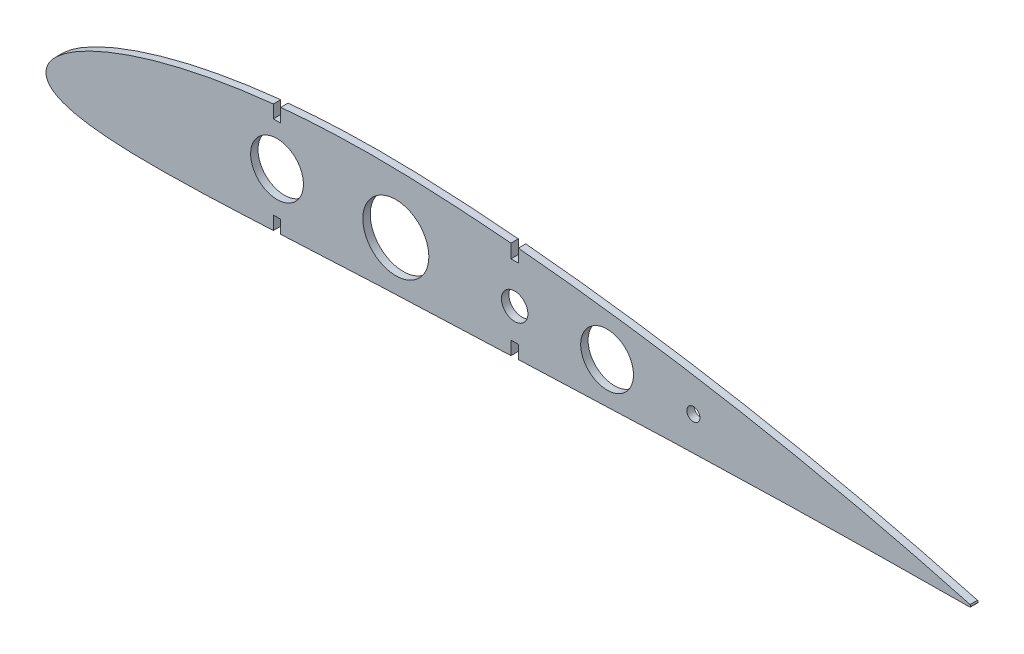
SolidWorks part; units mm, degrees
material "Сосна обыкновенная"
ref_plane "Front Plane" through (0, 0, 0) normal (0, 0, 1) x (1, 0, 0)
ref_plane "Top Plane" through (0, 0, 0) normal (0, 1, 0) x (1, 0, 0)
ref_plane "Right Plane" through (0, 0, 0) normal (1, 0, 0) x (0, 0, -1)
curve "Кривая1"
  spline degree 3 poles (0.0672, 0.87, 0) (0.0318, 0.5229, 0) (-0.0389, -0.1715, 0) (0.1092, -1.2382, 0) (0.4896, -2.2944, 0) (1.1401, -3.3111, 0) (2.0489, -4.255, 0) (3.2074, -5.1254, 0) (4.6283, -5.9301, 0) (6.3494, -6.6831, 0) (8.4416, -7.3951, 0) (11.0166, -8.0714, 0) (14.2364, -8.7104, 0) (18.3056, -9.2955, 0) (23.4194, -9.7901, 0) (29.6659, -10.1463, 0) (36.96, -10.3273, 0) (45.0764, -10.3268, 0) (53.7569, -10.166, 0) (62.8007, -9.8793, 0) (72.0812, -9.501, 0) (81.5234, -9.0613, 0) (91.0729, -8.586, 0) (100.6751, -8.0976, 0) (110.2799, -7.6156, 0) (119.8547, -7.1553, 0) (129.405, -6.7269, 0) (138.957, -6.3448, 0) (148.5363, -5.9896, 0) (158.1569, -5.6043, 0) (167.8102, -5.2124, 0) (177.4834, -4.8161, 0) (187.1542, -4.4222, 0) (196.8146, -4.0353, 0) (206.4608, -3.6595, 0) (216.0936, -3.2979, 0) (225.7151, -2.9531, 0) (235.3272, -2.6273, 0) (244.9322, -2.3221, 0) (254.532, -2.0389, 0) (264.1285, -1.7785, 0) (273.7233, -1.5416, 0) (283.3173, -1.3281, 0) (292.9097, -1.138, 0) (302.4935, -0.971, 0) (312.041, -0.8264, 0) (321.4647, -0.7041, 0) (330.5223, -0.6041, 0) (338.7731, -0.5271, 0) (345.1826, -0.4754, 0) (348.7687, -0.4498, 0) (350, -0.441, 0) knots 0 0 0 0 0.002941 0.005884 0.009016 0.012365 0.016008 0.020037 0.024574 0.029784 0.035897 0.04324 0.052276 0.063635 0.077983 0.095698 0.11652 0.139661 0.164312 0.189919 0.216157 0.242838 0.269834 0.296993 0.324123 0.351139 0.378036 0.404946 0.431961 0.459078 0.486347 0.513641 0.540929 0.568176 0.59538 0.622543 0.649673 0.676775 0.703855 0.730919 0.757971 0.785018 0.812062 0.839103 0.866132 0.893099 0.919831 0.94581 0.969681 0.98959 1 1 1 1
curve "Кривая2"
  spline degree 3 poles (350, 0.441, 0) (348.8179, 0.763, 0) (345.4082, 1.6919, 0) (339.3479, 3.3017, 0) (331.5897, 5.3027, 0) (323.0919, 7.4172, 0) (314.2383, 9.538, 0) (305.2428, 11.6083, 0) (296.1874, 13.6076, 0) (287.1014, 15.5293, 0) (277.9952, 17.371, 0) (268.8733, 19.1314, 0) (259.7387, 20.8097, 0) (250.5935, 22.4048, 0) (241.4399, 23.9153, 0) (232.28, 25.3398, 0) (223.1162, 26.6763, 0) (213.9505, 27.9228, 0) (204.7856, 29.077, 0) (195.6239, 30.1359, 0) (186.4686, 31.0968, 0) (177.3222, 31.956, 0) (168.1915, 32.7096, 0) (159.08, 33.3545, 0) (150.0138, 33.8803, 0) (141.0375, 34.2978, 0) (132.1765, 34.5613, 0) (123.4183, 34.6361, 0) (114.7287, 34.5224, 0) (106.0927, 34.2174, 0) (97.5152, 33.7146, 0) (89.0056, 33.0092, 0) (80.5773, 32.0949, 0) (72.2481, 30.9667, 0) (64.0422, 29.6192, 0) (55.9942, 28.0495, 0) (48.1571, 26.2588, 0) (40.6145, 24.2587, 0) (33.4961, 22.0806, 0) (26.979, 19.788, 0) (21.2507, 17.4767, 0) (16.4367, 15.2539, 0) (12.5431, 13.2014, 0) (9.4652, 11.352, 0) (7.0472, 9.6945, 0) (5.1404, 8.1959, 0) (3.6289, 6.8198, 0) (2.4334, 5.5336, 0) (1.4978, 4.3133, 0) (0.8003, 3.1383, 0) (0.3021, 2.0031, 0) (0.1432, 1.2365, 0) (0.0672, 0.87, 0) knots 0 0 0 0 0.010162 0.029313 0.052012 0.076619 0.101948 0.127526 0.153184 0.178868 0.204558 0.230246 0.255926 0.281594 0.307246 0.332878 0.358485 0.384061 0.409603 0.435104 0.460559 0.485959 0.511303 0.536552 0.561723 0.586629 0.611085 0.635251 0.659272 0.683164 0.706922 0.730536 0.753983 0.777235 0.800246 0.822951 0.845237 0.866916 0.887662 0.906968 0.924203 0.938879 0.950932 0.960693 0.968647 0.975233 0.980795 0.985584 0.989782 0.993521 0.996902 1 1 1 1
sketch "Эскиз2" plane through (0, 0, 0) normal (0, 0, 1) x (1, 0, 0)
  line L0 (350.1827, 0) -> (350.1827, 52.2565) construction
  line L1 (0, 0) -> (0, 59.698) construction
  line L2 (0, 0) -> (433.3101, 0) construction
  line L3 (87.5, 77.9689) -> (87.5, 51.797) construction
  line L4 (245.1827, 113.1345) -> (245.1827, -75.2237) construction
  line L5 (48.6093, 12.0313) -> (245.1827, 12.0313) construction
  line L10 (87.5, 32.8256) -> (87.5, -53.7006) construction
  line L12 (86.1, 32.6823) -> (86.1, 27.7856)
  line L13 (86.1, 27.7856) -> (88.9, 27.7856)
  line L14 (88.9, 32.963) -> (88.9, 27.7856)
  line L15 (87.5, 32.8256) -> (88.9, 27.7856) construction
  line L16 (86.1, 27.7856) -> (87.5, 32.8256) construction
  line L17 (177.5, 12.0313) -> (177.5, 39.9872) construction
  line L18 (177.5, 12.0313) -> (177.5, -23.4861) construction
  line L19 (176.1, 26.8829) -> (178.9, 26.8829)
  line L20 (176.1, 26.8829) -> (176.1, 32.0455)
  line L22 (178.9, 26.8829) -> (178.9, 31.7979)
  line L23 (176.1, 26.8829) -> (177.5, 31.9229) construction
  line L24 (177.5, 31.9229) -> (178.9, 26.8829) construction
  line L26 (86.1, -8.8326) -> (86.1, -3.7231)
  line L27 (86.1, -3.7231) -> (88.9, -3.7231)
  line L28 (88.9, -8.6933) -> (88.9, -3.7231)
  line L29 (87.5, -8.7631) -> (88.9, -3.7231) construction
  line L30 (86.1, -3.7231) -> (87.5, -8.7631) construction
  line L33 (176.1, -4.873) -> (176.1, 0.2242)
  line L34 (176.1, 0.2242) -> (178.9, 0.2242)
  line L35 (178.9, -4.7586) -> (178.9, 0.2242)
  line L36 (177.5, -4.8158) -> (178.9, 0.2242) construction
  line L37 (176.1, 0.2242) -> (177.5, -4.8158) construction
  arc A0 (350, 0.441) -> (350, -0.441) centre (349.559, 0) cw
  circle A5 centre (87.5, 12.0313) radius 10
  circle A6 centre (177.5, 12.0313) radius 5
  circle A7 centre (132.5, 12.0313) radius 12.5
  circle A8 centre (212.5, 12.0313) radius 10
  circle A10 centre (245.1827, 10.4878) radius 2.5
  spline S2 degree 3 poles (0.0672, 0.87) (0.0318, 0.5229) (-0.0389, -0.1715) (0.1092, -1.2382) (0.4896, -2.2944) (1.1401, -3.3111) (2.0489, -4.255) (3.2074, -5.1254) (4.6283, -5.9301) (6.3494, -6.6831) (8.4416, -7.3951) (11.0166, -8.0714) (14.2364, -8.7104) (18.3056, -9.2955) (23.4194, -9.7901) (29.6659, -10.1463) (36.96, -10.3273) (45.0764, -10.3268) (53.7569, -10.166) (62.8007, -9.8793) (72.0812, -9.501) (79.8719, -9.1382) (84.562, -8.9087) (86.1, -8.8326) knots 0 0 0 0 0.002941 0.005884 0.009016 0.012365 0.016008 0.020037 0.024574 0.029784 0.035897 0.04324 0.052276 0.063635 0.077983 0.095698 0.11652 0.139661 0.164312 0.189919 0.216157 0.242838 0.255856 0.255856 0.255856 0.255856
  spline S3 degree 3 poles (350, 0.441) (348.8179, 0.763) (345.4082, 1.6919) (339.3479, 3.3017) (331.5897, 5.3027) (323.0919, 7.4172) (314.2383, 9.538) (305.2428, 11.6083) (296.1874, 13.6076) (287.1014, 15.5293) (277.9952, 17.371) (268.8733, 19.1314) (259.7387, 20.8097) (250.5935, 22.4048) (241.4399, 23.9153) (232.28, 25.3398) (223.1162, 26.6763) (213.9505, 27.9228) (204.7856, 29.077) (195.6239, 30.1359) (186.9965, 31.0414) (181.4212, 31.5705) (178.9, 31.7979) knots 0 0 0 0 0.010162 0.029313 0.052012 0.076619 0.101948 0.127526 0.153184 0.178868 0.204558 0.230246 0.255926 0.281594 0.307246 0.332878 0.358485 0.384061 0.409603 0.435104 0.460559 0.481556 0.481556 0.481556 0.481556
  spline S4 degree 3 poles (88.9, -8.6933) (89.6178, -8.6574) (93.5441, -8.4603) (100.6751, -8.0976) (110.2799, -7.6156) (119.8547, -7.1553) (129.405, -6.7269) (138.957, -6.3448) (148.5363, -5.9896) (158.1569, -5.6043) (167.3488, -5.2312) (173.3358, -4.986) (176.1, -4.873) knots 0.263757 0.263757 0.263757 0.263757 0.269834 0.296993 0.324123 0.351139 0.378036 0.404946 0.431961 0.459078 0.486347 0.509737 0.509737 0.509737 0.509737
  spline S5 degree 3 poles (86.1, 32.6823) (84.251, 32.489) (79.6181, 31.965) (72.2481, 30.9667) (64.0422, 29.6192) (55.9942, 28.0495) (48.1571, 26.2588) (40.6145, 24.2587) (33.4961, 22.0806) (26.979, 19.788) (21.2507, 17.4767) (16.4367, 15.2539) (12.5431, 13.2014) (9.4652, 11.352) (7.0472, 9.6945) (5.1404, 8.1959) (3.6289, 6.8198) (2.4334, 5.5336) (1.4978, 4.3133) (0.8003, 3.1383) (0.3021, 2.0031) (0.1432, 1.2365) (0.0672, 0.87) knots 0.738563 0.738563 0.738563 0.738563 0.753983 0.777235 0.800246 0.822951 0.845237 0.866916 0.887662 0.906968 0.924203 0.938879 0.950932 0.960693 0.968647 0.975233 0.980795 0.985584 0.989782 0.993521 0.996902 1 1 1 1
  spline S6 degree 3 poles (178.9, -4.7586) (181.653, -4.6463) (187.6262, -4.4033) (196.8146, -4.0353) (206.4608, -3.6595) (216.0936, -3.2979) (225.7151, -2.9531) (235.3272, -2.6273) (244.9322, -2.3221) (254.532, -2.0389) (264.1285, -1.7785) (273.7233, -1.5416) (283.3173, -1.3281) (292.9097, -1.138) (302.4935, -0.971) (312.041, -0.8264) (321.4647, -0.7041) (330.5223, -0.6041) (338.7731, -0.5271) (345.1826, -0.4754) (348.7687, -0.4498) (350, -0.441) knots 0.517634 0.517634 0.517634 0.517634 0.540929 0.568176 0.59538 0.622543 0.649673 0.676775 0.703855 0.730919 0.757971 0.785018 0.812062 0.839103 0.866132 0.893099 0.919831 0.94581 0.969681 0.98959 1 1 1 1
  spline S7 degree 3 poles (176.1, 32.0455) (173.4606, 32.2744) (167.7863, 32.7382) (159.08, 33.3545) (150.0138, 33.8803) (141.0375, 34.2978) (132.1765, 34.5613) (123.4183, 34.6361) (114.7287, 34.5224) (106.0927, 34.2174) (97.4854, 33.7129) (91.7636, 33.2378) (88.9, 32.963) knots 0.489328 0.489328 0.489328 0.489328 0.511303 0.536552 0.561723 0.586629 0.611085 0.635251 0.659272 0.683164 0.706922 0.730783 0.730783 0.730783 0.730783
  point P14 (87.5, 32.8256)
  point P17 (87.5, -8.7631)
  point P26 (87.5, 32.8256)
  point P28 (177.5, 31.9229)
  point P35 (177.5, 31.9229)
  point P36 (87.5, -8.7631)
  point P42 (87.5, -8.7631)
  point P46 (177.5, -4.8158)
  point P49 (177.5, -4.8158)
  point P54 (245.1827, 23.2937)
  point P57 (245.1827, -2.3181)
  dimension "D1" = 0.6237
  dimension "D5" = 20
  dimension "D8" = 10
  dimension "D10" = 25
  dimension "D12" = 20
  dimension "D26" = 5
  dimension "D2" = 350.1827
  dimension "D4" = 105
  dimension "D3" = 87.5
  dimension "D6" = 41.5887
  dimension "D7" = 20.7944
  dimension "D9" = 90
  dimension "D11" = 45
  dimension "D13" = 35
  dimension "D14" = 2.8
  dimension "D15" = 1.4
  dimension "D16" = 5.04
  dimension "D17" = 2.8
  dimension "D18" = 1.4
  dimension "D19" = 5.04
  dimension "D20" = 2.8
  dimension "D21" = 5.04
  dimension "D22" = 1.4
  dimension "D23" = 2.8
  dimension "D24" = 5.04
  dimension "D25" = 1.4
extrude "Бобышка-Вытянуть1" add sketch "Эскиз2" along normal mid plane 2.8
equation "\"Thickness\"= 2.8"
equation "\"chord\"= 350"
equation "\"D4@Эскиз2\"=\"chord\"*0.3"
equation "\"D3@Эскиз2\"=\"chord\"/4"
equation "\"D7@Эскиз2\"=\"D6@Эскиз2\"/2"
equation "\"D11@Эскиз2\"=\"D9@Эскиз2\"/2"
equation "\"D14@Эскиз2\"=\"Thickness\""
equation "\"D15@Эскиз2\"=\"D14@Эскиз2\"/2"
equation "\"D16@Эскиз2\"=\"Thickness\"*1.8"
equation "\"D17@Эскиз2\"=\"Thickness\""
equation "\"D18@Эскиз2\"=\"Thickness\"/2"
equation "\"D19@Эскиз2\"=\"Thickness\"*1.8"
equation "\"D20@Эскиз2\"=\"Thickness\""
equation "\"D21@Эскиз2\"=\"Thickness\"*1.8"
equation "\"D22@Эскиз2\"=\"Thickness\"/2"
equation "\"D23@Эскиз2\"=\"Thickness\""
equation "\"D24@Эскиз2\"=\"Thickness\"*1.8"
equation "\"D25@Эскиз2\"=\"Thickness\"/2"
